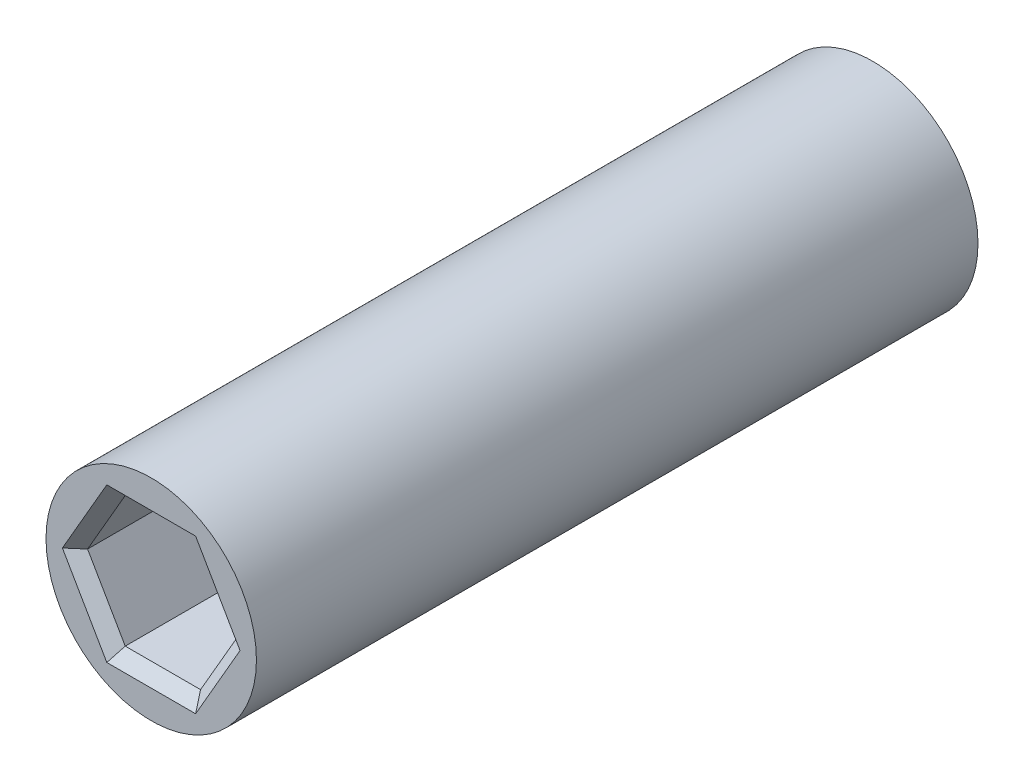
SolidWorks part; units mm, degrees
ref_plane "Front Plane" through (0, 0, 0) normal (0, 0, 1) x (1, 0, 0)
ref_plane "Top Plane" through (0, 0, 0) normal (0, 1, 0) x (1, 0, 0)
ref_plane "Right Plane" through (0, 0, 0) normal (1, 0, 0) x (0, 0, -1)
sketch "Sketch1" plane through (0, 0, 0) normal (0, 1, 0) x (1, 0, 0)
  line L0 (0, 0) -> (0, 65.86) construction
  line L1 (0, 48.36) -> (0, 17.5)
  point P3 (0, 41.86)
  point P4 (0, 24)
  point P5 (0, 48.36)
  point P6 (0, 17.5)
  dimension "D1" = 65.86
  dimension "D2" = 24
  dimension "D3" = 24
  dimension "D4" = 17.86
  dimension "D5" = 6.5
  dimension "D6" = 6.5
revolve "Revolve-Thin1" add sketch "Sketch1" angle 360 about L0 wall 4.5
sketch "Sketch2" plane through (0, 0, -17.5) normal (0, 0, 1) x (1, 0, 0)
  line L1 (1.6108, 2.79) -> (-1.6108, 2.79)
  line L2 (-1.6108, 2.79) -> (-3.2216, 0)
  line L3 (-3.2216, 0) -> (-1.6108, -2.79)
  line L4 (-1.6108, -2.79) -> (1.6108, -2.79)
  line L5 (1.6108, -2.79) -> (3.2216, 0)
  line L6 (3.2216, 0) -> (1.6108, 2.79)
  circle A0 centre (0, 0) radius 2.79 construction
  dimension "D1" = 5.58
extrude "Cut-Extrude1" cut sketch "Sketch2" against normal blind 7
sketch "Sketch3" plane through (0, 0, -48.36) normal (0, 0, -1) x (-1, 0, 0)
  line L1 (1.6108, 2.79) -> (-1.6108, 2.79)
  line L2 (-1.6108, 2.79) -> (-3.2216, 0)
  line L3 (-3.2216, 0) -> (-1.6108, -2.79)
  line L4 (-1.6108, -2.79) -> (1.6108, -2.79)
  line L5 (1.6108, -2.79) -> (3.2216, 0)
  line L6 (3.2216, 0) -> (1.6108, 2.79)
  circle A0 centre (0, 0) radius 2.79 construction
  dimension "D1" = 5.58
extrude "Cut-Extrude2" cut sketch "Sketch3" against normal blind 7
chamfer "Chamfer1" distance 0.5 angle 45 12 edges at (2.4162, 1.395, -17.5) (2.4162, -1.395, -17.5) (0, -2.79, -17.5) (-2.4162, -1.395, -17.5) (-2.4162, 1.395, -17.5) (0, 2.79, -17.5) (0, 2.79, -48.36) (-2.4162, 1.395, -48.36) (-2.4162, -1.395, -48.36) (0, -2.79, -48.36) (2.4162, -1.395, -48.36) (2.4162, 1.395, -48.36)
sketch3d "3DSketch1" plane through (0, 0, 0) normal (0, 0, 1) x (1, 0, 0)
sketch "Sketch4" plane through (0, -4.5, 0) normal (0, 1, 0) x (1, 0, 0)
  line L0 (-4.5, 17.5) -> (4.5, 17.5) construction
  line L1 (4.5, 48.36) -> (-4.5, 48.36) construction
  line L2 (-4.5, 17.5) -> (4.5, 17.5) construction
  line L3 (4.5, 48.36) -> (-4.5, 48.36) construction
  line L4 (-4.5, 17.5) -> (-4.5, 48.36) construction
  line L5 (4.5, 48.36) -> (4.5, 17.5) construction
  line L6 (-4.5, 32.93) -> (4.5, 32.93) construction
  text T0 "<b><i>R</i></b>"
extrude "Cut-Extrude3" cut sketch "Sketch4" along normal blind 1
